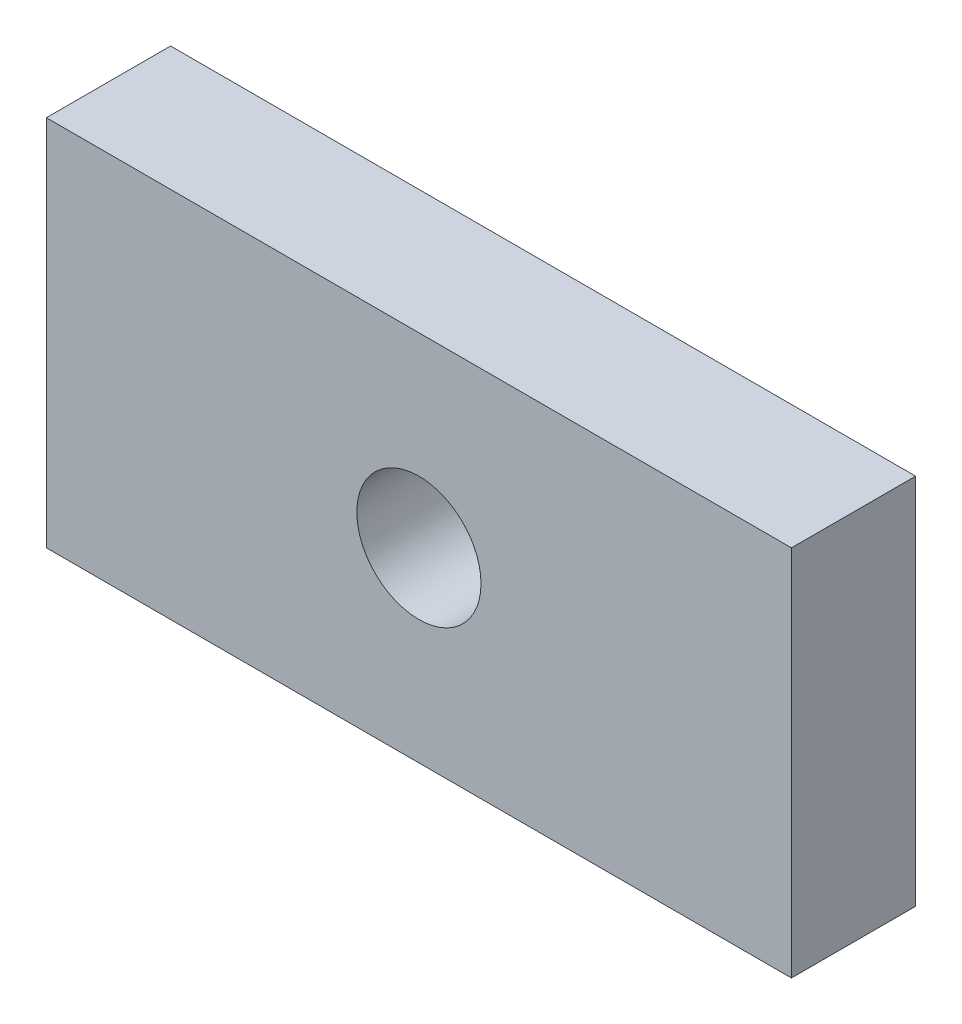
SolidWorks part; units mm, degrees
ref_plane "Front Plane" through (0, 0, 0) normal (0, 0, 1) x (1, 0, 0)
ref_plane "Top Plane" through (0, 0, 0) normal (0, 1, 0) x (1, 0, 0)
ref_plane "Right Plane" through (0, 0, 0) normal (1, 0, 0) x (0, 0, -1)
sketch "Sketch1" plane through (0, 0, 0) normal (0, 0, 1) x (1, 0, 0)
  line L1 (0, 0) -> (76.2, 0)
  line L2 (0, 0) -> (0, 38.1)
  line L3 (0, 38.1) -> (76.2, 38.1)
  line L4 (76.2, 0) -> (76.2, 38.1)
  circle A0 centre (38.1, 19.05) radius 6.35
  dimension "D3" = 12.7
  dimension "D1" = 38.1
  dimension "D2" = 76.2
  dimension "D4" = 38.1
  dimension "D5" = 19.05
extrude "Boss-Extrude1" add sketch "Sketch1" along normal blind 12.7
